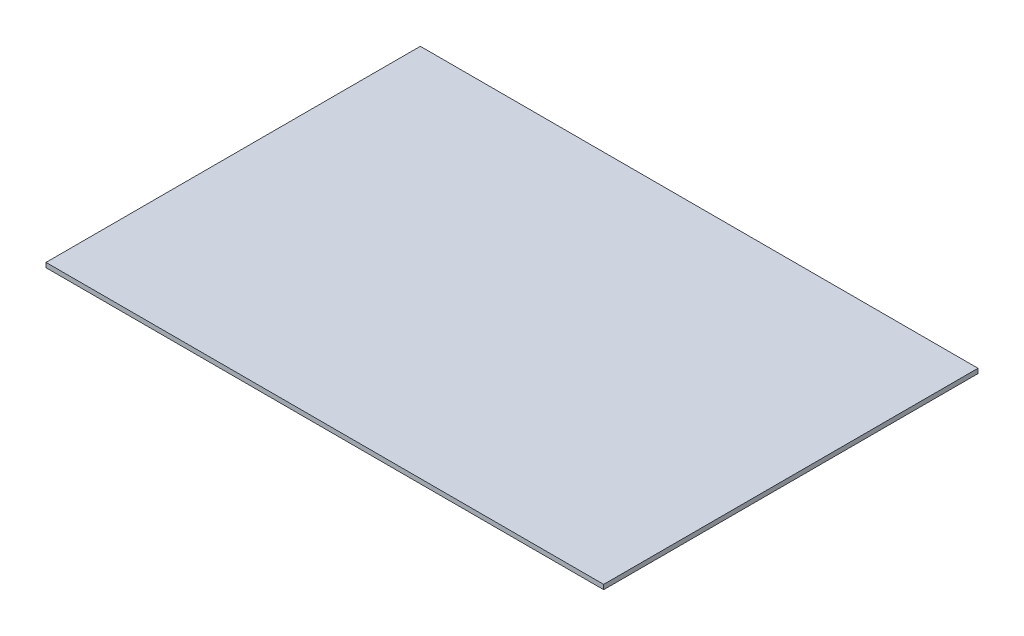
SolidWorks part; units mm, degrees
ref_plane "Front Plane" through (0, 0, 0) normal (0, 0, 1) x (1, 0, 0)
ref_plane "Top Plane" through (0, 0, 0) normal (0, 1, 0) x (1, 0, 0)
ref_plane "Right Plane" through (0, 0, 0) normal (1, 0, 0) x (0, 0, -1)
sketch "Sketch1" plane through (0, 0, 0) normal (0, 1, 0) x (1, 0, 0)
  line L1 (-10.16, -10.16) -> (600, -10.16)
  line L2 (-10.16, -10.16) -> (-10.16, 399.38)
  line L3 (-10.16, 399.38) -> (600, 399.38)
  line L4 (600, -10.16) -> (600, 399.38)
  point P5 (0, 0)
  point P6 (-10.16, -10.16)
  point P8 (0, 0)
  point P9 (-10.16, 399.38)
  point P12 (600, -10.16)
  dimension "D1" = 409.54
  dimension "D2" = 610.16
extrude "Boss-Extrude1" add sketch "Sketch1" along normal blind 5.08
